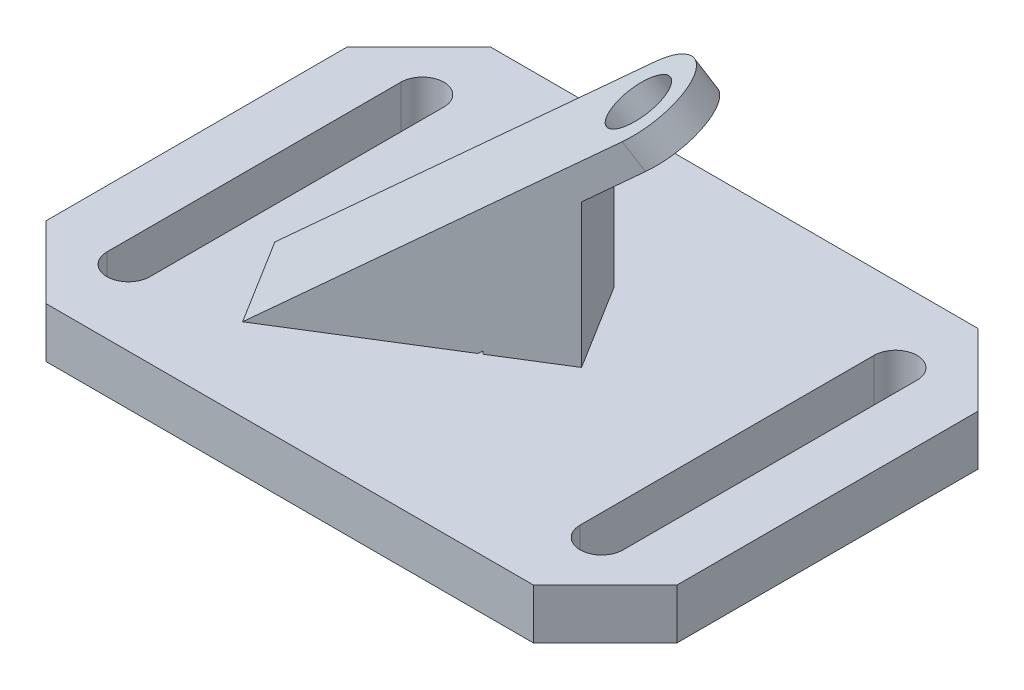
SolidWorks part; units mm, degrees
material "Alloy Steel"
ref_plane "Front Plane" through (0, 0, 0) normal (0, 0, 1) x (1, 0, 0)
ref_plane "Top Plane" through (0, 0, 0) normal (0, 1, 0) x (1, 0, 0)
ref_plane "Right Plane" through (0, 0, 0) normal (1, 0, 0) x (0, 0, -1)
sketch "Sketch1" plane through (0, 0, 0) normal (0, 1, 0) x (1, 0, 0)
  line L0 (34, 31) -> (44, 21)
  line L1 (-34, -31) -> (34, -31)
  line L2 (-44, -21) -> (-44, 21)
  line L3 (-34, 31) -> (34, 31)
  line L4 (44, -21) -> (44, 21)
  line L5 (-44, -31) -> (44, 31) construction
  line L6 (-44, 31) -> (44, -31) construction
  line L7 (-44, 21) -> (-34, 31)
  line L8 (-44, -21) -> (-34, -31)
  line L9 (34, -31) -> (44, -21)
  line L10 (-33, 20.5) -> (-33, -20.5) construction
  line L11 (-30, 20.5) -> (-30, -20.5)
  line L12 (-36, 20.5) -> (-36, -20.5)
  line L13 (33, 20.5) -> (33, -20.5) construction
  line L14 (36, 20.5) -> (36, -20.5)
  line L15 (30, 20.5) -> (30, -20.5)
  arc A0 (-30, 20.5) -> (-36, 20.5) centre (-33, 20.5) ccw
  arc A1 (-36, -20.5) -> (-30, -20.5) centre (-33, -20.5) ccw
  arc A2 (36, 20.5) -> (30, 20.5) centre (33, 20.5) ccw
  arc A3 (30, -20.5) -> (36, -20.5) centre (33, -20.5) ccw
  point P0 (0, 0)
  point P16 (-33, 0)
  point P21 (33, 0)
  dimension "D1" = 88
  dimension "D2" = 62
  dimension "D3" = 8
  dimension "D4" = 10.5
  dimension "D9" = 6
  dimension "D10" = 41
  dimension "D11" = 8
  dimension "D12" = 10.5
  dimension "D13" = 6
extrude "Boss-Extrude1" add sketch "Sketch1" along normal blind 7
sketch "Sketch2" plane through (0, 7, 0) normal (0, 1, 0) x (1, 0, 0)
  line L0 (-33, -20.5) -> (33, 20.5) construction
ref_plane "Plane1" through (0, 0, 0) normal (0.5277, 0, 0.8494) x (0.8494, 0, -0.5277)
sketch "Sketch3" plane through (0, 0, 0) normal (0.5277, 0, 0.8494) x (0.8494, 0, -0.5277)
  line L0 (-18.8491, 7) -> (8.6786, 27)
  line L1 (-38.8491, 7) -> (38.8491, 7) construction
  line L2 (8.6786, 27) -> (8.6786, 7)
  point P7 (13.2142, 27)
  dimension "D1" = 20
  dimension "D2" = 36
  dimension "D3" = 20
extrude "Extrude-Thin1" add sketch "Sketch3" along normal mid plane 14 thin
sketch "Sketch4" plane through (-8.3593, 13.5448, 5.1929) normal (-0.4993, 0.809, 0.3102) x (0.8664, 0.4662, 0.1787)
  line L0 (20.2382, 24.3657) -> (-17.8536, -4.8835)
  line L1 (-17.8536, -4.8835) -> (-9.3272, -15.9876)
  line L4 (22.0653, 21.9863) -> (26.9375, 15.6411) construction
  line L5 (28.7646, 13.2616) -> (-9.3272, -15.9876)
  line L6 (-4.5683, -12.3334) -> (22.4194, 8.3894) construction
  line L7 (-13.0947, -1.2293) -> (13.893, 19.4935) construction
  line L8 (-4.5683, -12.3334) -> (-13.0947, -1.2293) construction
  line L12 (22.4194, 8.3894) -> (13.893, 19.4935) construction
  arc A0 (28.7646, 13.2616) -> (20.2382, 24.3657) centre (24.5014, 18.8137) ccw
  circle A1 centre (24.5014, 18.8137) radius 4
  point P16 (27.5443, 14.8508)
  point P17 (0, 0)
  point P18 (29.9282, 14.1551)
  point P19 (0, 0)
  dimension "D3" = 8
  dimension "D1" = 6
  dimension "D2" = 8
  dimension "D4" = 8
extrude "Boss-Extrude2" add sketch "Sketch4" along normal blind 4
